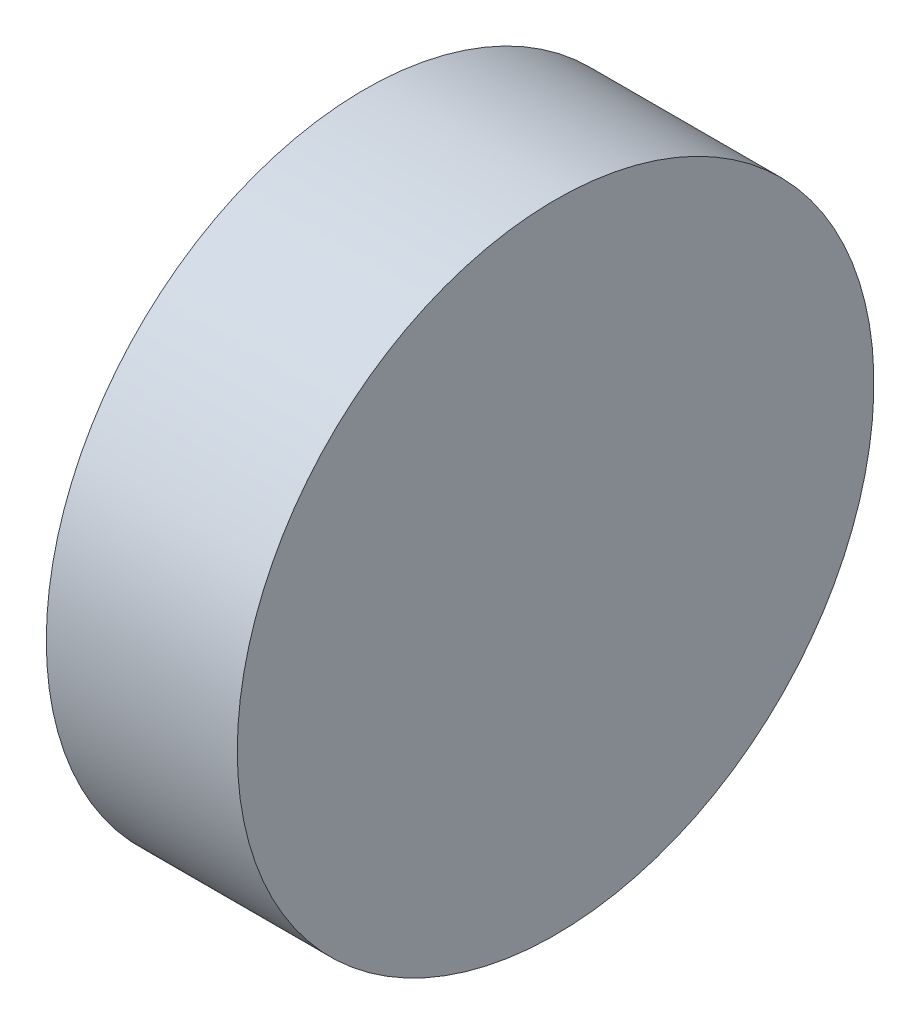
SolidWorks part; units mm, degrees
ref_plane "前视基准面" through (0, 0, 0) normal (0, 0, 1) x (1, 0, 0)
ref_plane "上视基准面" through (0, 0, 0) normal (0, 1, 0) x (1, 0, 0)
ref_plane "右视基准面" through (0, 0, 0) normal (1, 0, 0) x (0, 0, -1)
sketch "草图1" plane through (0, 0, 0) normal (0, 0, 1) x (1, 0, 0)
  line L0 (127.0004, 38.6466) -> (139.6266, 38.6466) construction
  line L1 (130.1009, 38.6466) -> (130.1009, 48.6466)
  line L2 (130.1009, 48.6466) -> (136.1009, 48.6466)
  line L3 (136.1009, 48.6466) -> (136.1009, 38.6466)
  line L4 (136.1009, 38.6466) -> (130.1009, 38.6466)
revolve "旋转1" add sketch "草图1" angle 360 about L0
